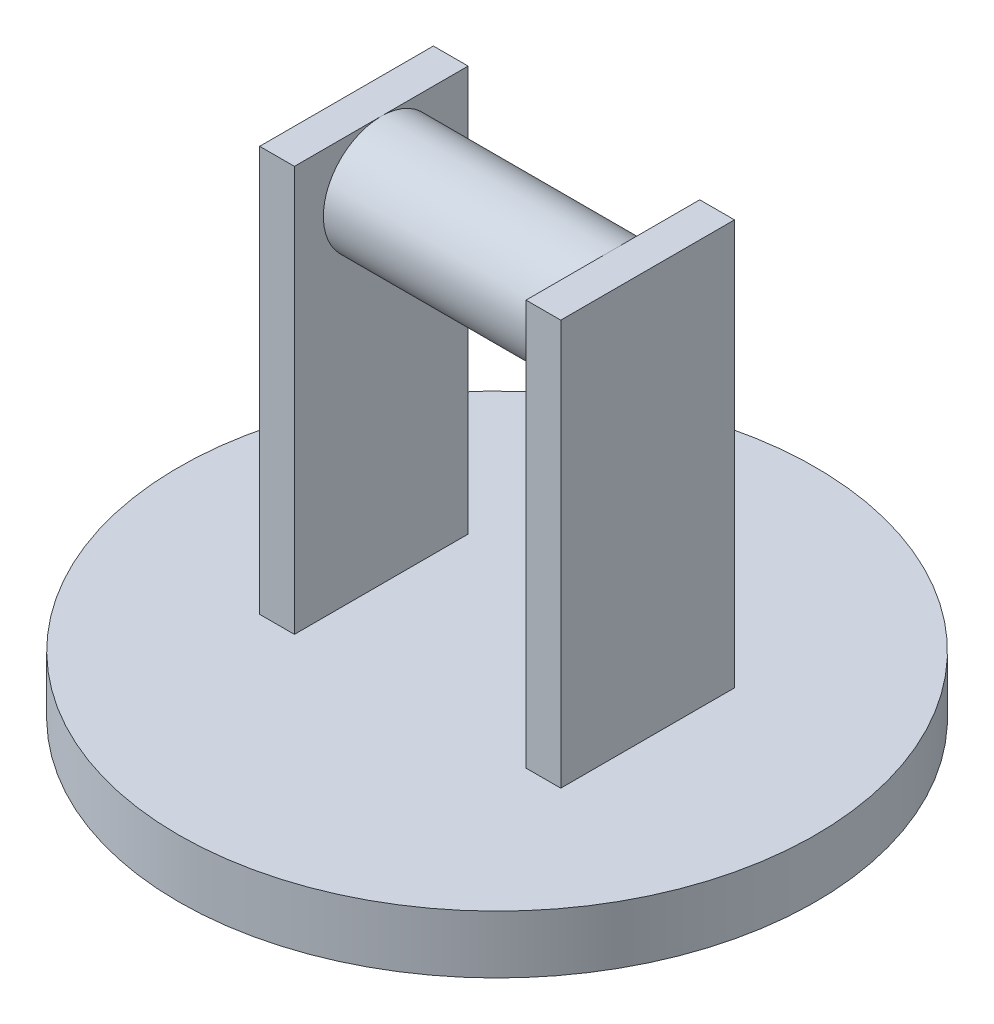
SolidWorks part; units mm, degrees
ref_plane "Front Plane" through (0, 0, 0) normal (0, 0, 1) x (1, 0, 0)
ref_plane "Top Plane" through (0, 0, 0) normal (0, 1, 0) x (1, 0, 0)
ref_plane "Right Plane" through (0, 0, 0) normal (1, 0, 0) x (0, 0, -1)
sketch "Sketch1" plane through (0, 0, 0) normal (0, 1, 0) x (1, 0, 0)
  circle A0 centre (0, 0) radius 34.925
  dimension "D1" = 69.85
extrude "Boss-Extrude1" add sketch "Sketch1" along normal blind 6.35
sketch "Sketch2" plane through (0, 6.35, 0) normal (0, 1, 0) x (1, 0, 0)
  line L1 (-12.7, -9.525) -> (12.7, -9.525)
  line L2 (-12.7, -9.525) -> (-12.7, 9.525)
  line L3 (-12.7, 9.525) -> (12.7, 9.525)
  line L4 (12.7, -9.525) -> (12.7, 9.525)
  line L5 (-12.7, -9.525) -> (12.7, 9.525) construction
  line L6 (-12.7, 9.525) -> (12.7, -9.525) construction
  line L7 (12.7, 9.525) -> (16.51, 9.525)
  line L8 (12.7, 9.525) -> (12.7, -9.525)
  line L9 (12.7, -9.525) -> (16.51, -9.525)
  line L10 (16.51, 9.525) -> (16.51, -9.525)
  line L11 (-12.7, 9.525) -> (-16.51, 9.525)
  line L12 (-12.7, 9.525) -> (-12.7, -9.525)
  line L13 (-12.7, -9.525) -> (-16.51, -9.525)
  line L14 (-16.51, 9.525) -> (-16.51, -9.525)
  point P0 (0, 0)
  dimension "D1" = 25.4
  dimension "D2" = 19.05
  dimension "D3" = 3.81
  dimension "D4" = 3.81
extrude "Boss-Extrude2" add sketch "Sketch2" along normal blind 44.45 contours L11 L14 L13 L2 | L10 L7 L4 L9
sketch "Sketch3" plane through (-12.7, 0, 0) normal (1, 0, 0) x (0, 0, -1)
  line L0 (-9.525, 50.8) -> (0, 50.8)
  line L1 (-9.525, 50.8) -> (9.525, 50.8) construction
  line L2 (0, 50.8) -> (0, 44.45)
  circle A0 centre (0, 44.45) radius 6.35
  dimension "D2" = 12.7
  dimension "D1" = 6.35
extrude "Boss-Extrude3" add sketch "Sketch3" along normal up to surface (25.4 mm away) up to face at (12.7, 28.575, 0)
